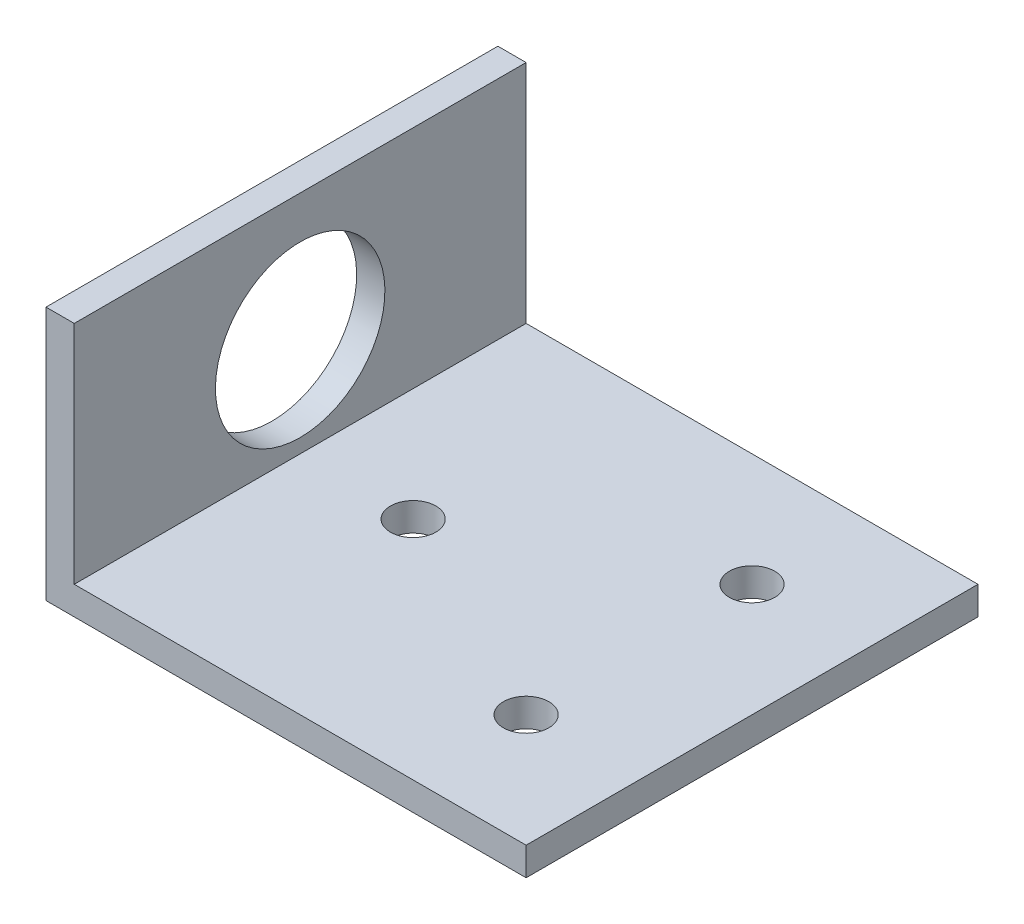
SolidWorks part; units mm, degrees
ref_plane "Front Plane" through (0, 0, 0) normal (0, 0, 1) x (1, 0, 0)
ref_plane "Top Plane" through (0, 0, 0) normal (0, 1, 0) x (1, 0, 0)
ref_plane "Right Plane" through (0, 0, 0) normal (1, 0, 0) x (0, 0, -1)
sketch "Sketch1" plane through (0, 0, 0) normal (0, 0, 1) x (1, 0, 0)
  line L1 (3.175, 50.8) -> (0, 50.8)
  line L2 (3.175, 50.8) -> (3.175, 3.175)
  line L3 (3.175, 0) -> (0, 0)
  line L4 (0, 50.8) -> (0, 0)
  line L5 (3.175, 0) -> (53.975, 0)
  line L7 (3.175, 3.175) -> (53.975, 3.175)
  line L8 (53.975, 0) -> (53.975, 3.175)
  dimension "D1" = 50.8
  dimension "D2" = 50.8
  dimension "D3" = 3.175
  dimension "D4" = 3.175
extrude "Boss-Extrude1" add sketch "Sketch1" along normal blind 50.8
sketch "Sketch2" plane through (0, 0, 0) normal (-1, 0, 0) x (0, 0, 1)
  line L0 (50.8, 0) -> (0, 0) construction
  line L1 (0, 50.8) -> (0, 0) construction
  line L2 (50.8, 50.8) -> (0, 50.8)
  line L3 (50.8, 50.8) -> (50.8, 28.575)
  line L4 (50.8, 28.575) -> (0, 28.575)
  line L5 (0, 50.8) -> (0, 28.575)
  line L6 (25.4, 0) -> (25.4, 28.575) construction
  circle A0 centre (25.4, 14.2875) radius 9.525
  point P4 (25.4, 0)
  dimension "D2" = 19.05
  dimension "D3" = 22.225
extrude "Cut-Extrude1" cut sketch "Sketch2" against normal blind 50.8
sketch "Sketch3" plane through (0, 0, 0) normal (0, -1, 0) x (-1, 0, 0)
  line L0 (0, -50.8) -> (0, 0) construction
  line L1 (-41.275, -38.1) -> (-41.275, -12.7) construction
  circle A0 centre (-15.875, -25.4) radius 2.5527
  circle A1 centre (-41.275, -38.1) radius 2.5527
  circle A2 centre (-41.275, -12.7) radius 2.5527
  point P8 (0, -25.4)
  point P9 (-41.275, -25.4)
  dimension "D1" = 5.1054
  dimension "D2" = 15.875
  dimension "D3" = 41.275
  dimension "D4" = 25.4
extrude "Cut-Extrude2" cut sketch "Sketch3" against normal blind 50.8
